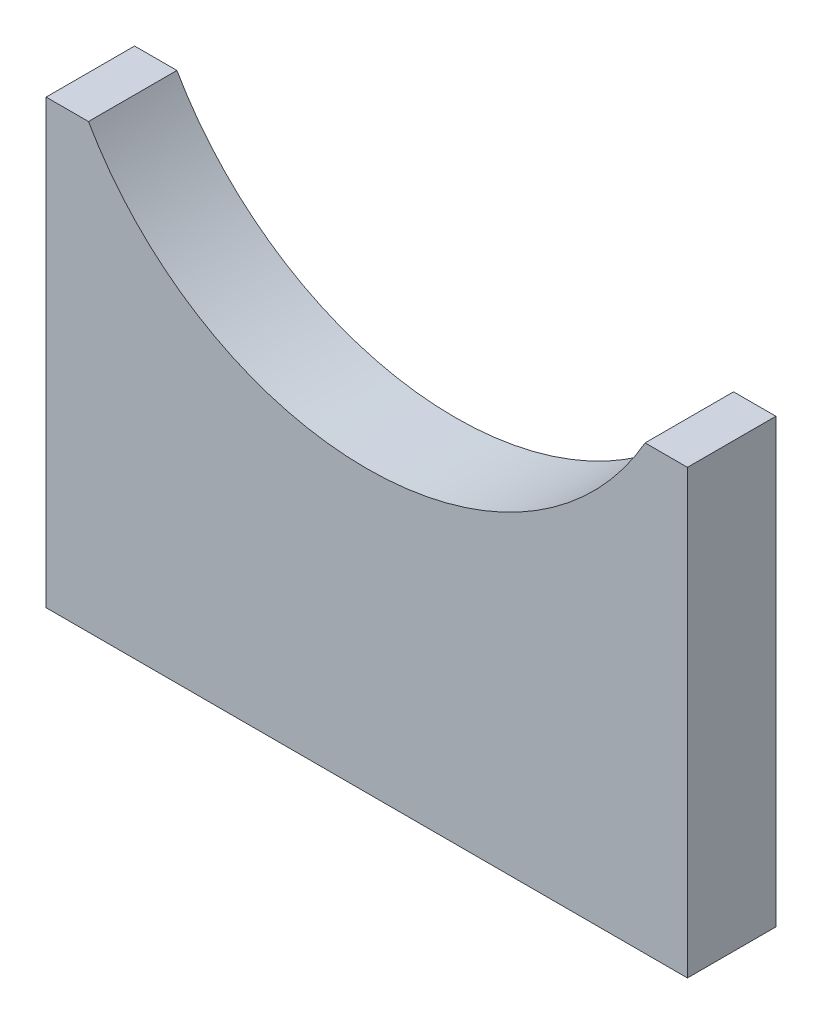
SolidWorks part; units mm, degrees
material "1060 Alloy"
ref_plane "Front Plane" through (0, 0, 0) normal (0, 0, 1) x (1, 0, 0)
ref_plane "Top Plane" through (0, 0, 0) normal (0, 1, 0) x (1, 0, 0)
ref_plane "Right Plane" through (0, 0, 0) normal (1, 0, 0) x (0, 0, -1)
sketch "Sketch1" plane through (0, 0, 0) normal (0, 0, 1) x (1, 0, 0)
  line L0 (-46.0375, 0) -> (46.0375, 0) construction
  line L1 (46.0375, 0) -> (46.0375, 86.36) construction
  line L2 (-46.0375, 86.36) -> (-46.0375, 0) construction
  line L3 (-46.0375, 63.5) -> (-39.9609, 63.5)
  line L4 (39.9609, 63.5) -> (46.0375, 63.5)
  line L5 (46.0375, 63.5) -> (46.0375, 0)
  line L6 (46.0375, 0) -> (-46.0375, 0)
  line L7 (-46.0375, 0) -> (-46.0375, 63.5)
  arc A0 (46.0375, 86.36) -> (-46.0375, 86.36) centre (0, 86.36) cw construction
  arc A1 (-39.9609, 63.5) -> (39.9609, 63.5) centre (0, 86.36) ccw
  dimension "D1" = 92.075
  dimension "D2" = 86.36
  dimension "D3" = 63.5
extrude "Boss-Extrude1" add sketch "Sketch1" along normal mid plane 12.7
sketch "Sketch2" plane through (0, 0, 0) normal (0, -1, 0) x (1, 0, 0)
  line L0 (-38.1, 0) -> (38.1, 0) construction
  circle A0 centre (-38.1, 0) radius 3.3655
  circle A1 centre (38.1, 0) radius 3.3655
  point P4 (0, 0)
  dimension "D1" = 6.731
  dimension "D2" = 76.2
extrude "Cut-Extrude1" cut sketch "Sketch2" against normal blind 12.7
sketch3d "TAG"
  line L0 (-46.0375, 0, 6.35) -> (-46.0375, 0, -6.35) construction
  line L1 (-46.0375, 63.5, 6.35) -> (-46.0375, 0, 6.35) construction
  line L2 (-46.0375, 0, 6.35) -> (46.0375, 0, 6.35) construction
  line L3 (-46.0375, 0, 6.35) -> (-46.0375, 0, -6.35)
  line L4 (-46.0375, 63.5, 6.35) -> (-46.0375, 0, 6.35)
  line L5 (-46.0375, 0, 6.35) -> (46.0375, 0, 6.35)
  dimension "D1" = 12.7
  dimension "D3" = 92.075
  dimension "D2" = 63.5
